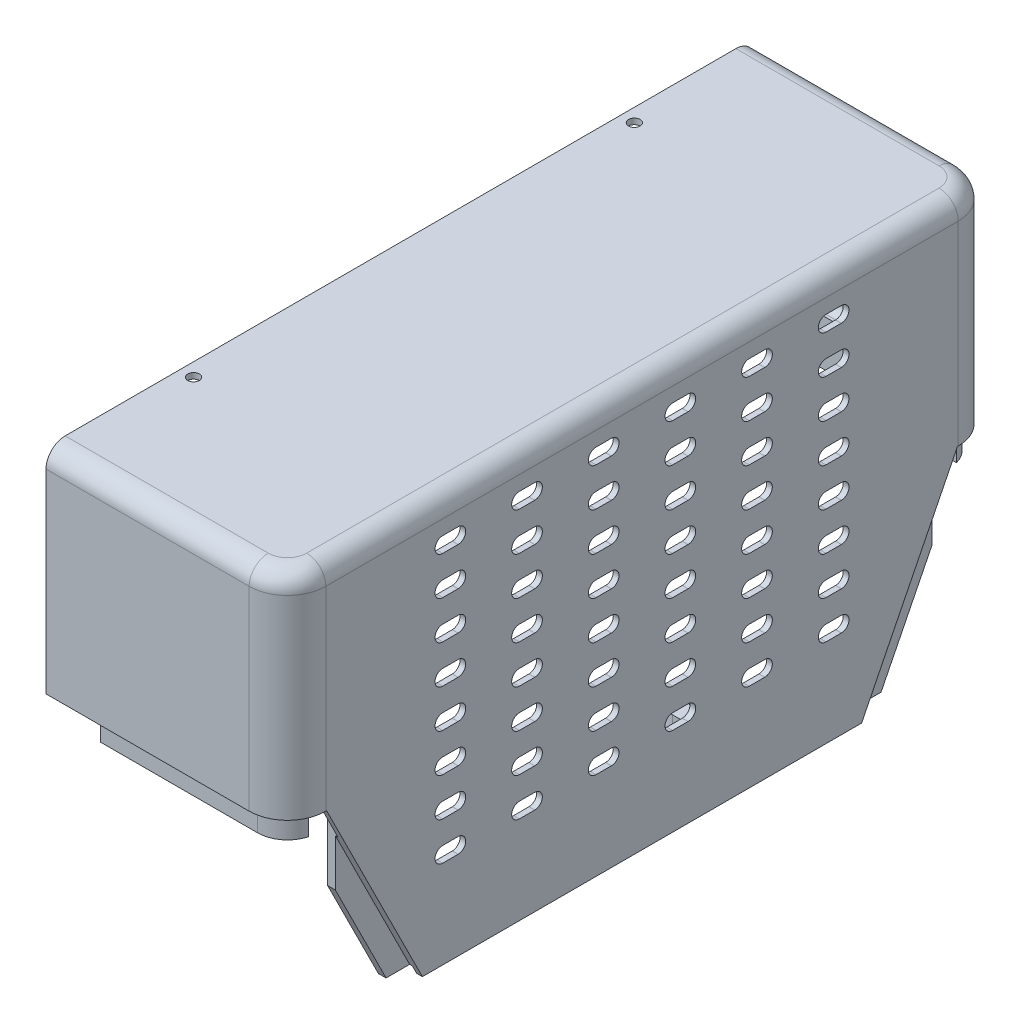
SolidWorks part; units mm, degrees
ref_plane "Alzado" through (0, 0, 0) normal (0, 0, 1) x (1, 0, 0)
ref_plane "Planta" through (0, 0, 0) normal (0, 1, 0) x (1, 0, 0)
ref_plane "Vista lateral" through (0, 0, 0) normal (1, 0, 0) x (0, 0, -1)
sketch "Croquis1" plane through (0, 60.8505, 0) normal (0, 1, 0) x (1, 0, 0)
  line L0 (-39.0358, -277.5) -> (-39.0358, -272.5) construction
  line L1 (-39.0358, -97.5) -> (-39.0358, -92.5) construction
  line L2 (-39.0358, -272.5) -> (-39.0358, -97.5) construction
  line L3 (13.9642, -92.5) -> (-39.0358, -92.5) construction
  line L4 (23.9642, -127.5) -> (23.9642, -102.5) construction
  line L5 (23.9642, -242.5) -> (23.9642, -127.5) construction
  line L6 (23.9642, -267.5) -> (23.9642, -242.5) construction
  line L7 (-39.0358, -277.5) -> (13.9642, -277.5) construction
  line L8 (-39.0358, -277.5) -> (-39.0358, -272.5)
  line L9 (-39.0358, -97.5) -> (-39.0358, -92.5)
  line L10 (-39.0358, -272.5) -> (-39.0358, -97.5)
  line L11 (13.9642, -92.5) -> (-39.0358, -92.5)
  line L12 (23.9642, -127.5) -> (23.9642, -102.5)
  line L13 (23.9642, -242.5) -> (23.9642, -127.5)
  line L14 (23.9642, -267.5) -> (23.9642, -242.5)
  line L15 (-39.0358, -277.5) -> (13.9642, -277.5)
  arc A0 (23.9642, -102.5) -> (13.9642, -92.5) centre (13.9642, -102.5) ccw construction
  arc A1 (13.9642, -277.5) -> (23.9642, -267.5) centre (13.9642, -267.5) ccw construction
  arc A2 (23.9642, -102.5) -> (13.9642, -92.5) centre (13.9642, -102.5) ccw
  arc A3 (13.9642, -277.5) -> (23.9642, -267.5) centre (13.9642, -267.5) ccw
extrude "Saliente-Extruir1" add sketch "Croquis1" against normal blind 1.5
sketch "Croquis2" plane through (0, 59.3505, 0) normal (0, -1, 0) x (1, 0, 0)
  line L0 (13.9642, 92.5) -> (-39.0358, 92.5) construction
  line L1 (23.9642, 267.5) -> (23.9642, 102.5) construction
  line L2 (-39.0358, 277.5) -> (13.9642, 277.5) construction
  line L3 (13.9642, 92.5) -> (-39.0358, 92.5)
  line L4 (23.9642, 267.5) -> (23.9642, 102.5)
  line L5 (-39.0358, 277.5) -> (13.9642, 277.5)
  line L6 (-39.0358, 276) -> (13.9642, 276)
  line L7 (22.4642, 267.5) -> (22.4642, 102.5)
  line L8 (13.9642, 94) -> (-39.0358, 94)
  line L9 (-39.0358, 92.5) -> (-39.0358, 94)
  line L10 (-39.0358, 277.5) -> (-39.0358, 276)
  arc A0 (13.9642, 92.5) -> (23.9642, 102.5) centre (13.9642, 102.5) ccw construction
  arc A1 (23.9642, 267.5) -> (13.9642, 277.5) centre (13.9642, 267.5) ccw construction
  arc A2 (13.9642, 92.5) -> (23.9642, 102.5) centre (13.9642, 102.5) ccw
  arc A3 (23.9642, 267.5) -> (13.9642, 277.5) centre (13.9642, 267.5) ccw
  arc A4 (22.4642, 267.5) -> (13.9642, 276) centre (13.9642, 267.5) ccw
  arc A5 (13.9642, 94) -> (22.4642, 102.5) centre (13.9642, 102.5) ccw
  dimension "D1" = 1.5
extrude "Saliente-Extruir2" add sketch "Croquis2" along normal offset from surface (54.3 mm away) 0.2
sketch "Croquis3" plane through (0, 5.0505, 0) normal (0, -1, 0) x (1, 0, 0)
  line L0 (22.4642, 267.3) -> (23.9642, 267.3)
  line L1 (22.4642, 102.5) -> (22.4642, 267.5) construction
  line L2 (23.9642, 267.5) -> (23.9642, 102.5) construction
  line L3 (23.9642, 267.3) -> (23.9642, 102.7)
  line L4 (23.9642, 102.7) -> (22.4642, 102.7)
  line L5 (22.4642, 102.7) -> (22.4642, 267.3)
  line L6 (21.9642, 267.5) -> (23.9642, 267.5) construction
  line L7 (23.9642, 102.5) -> (21.9642, 102.5) construction
  dimension "D1" = 0.2
  dimension "D2" = 0.2
extrude "Saliente-Extruir3" add sketch "Croquis3" along normal offset from surface (50 mm away) 0.2
sketch "Croquis4" plane through (23.9642, 0, 0) normal (1, 0, 0) x (0, 0, -1)
  line L0 (-267.3, 5.0505) -> (-242.3, -44.9495)
  line L1 (-102.7, -44.9495) -> (-267.3, -44.9495) construction
  line L2 (-242.3, -44.9495) -> (-280.9783, -56.8361)
  line L3 (-280.9783, -56.8361) -> (-267.3, 5.0505)
  line L4 (-102.7, 5.0505) -> (-131.2482, -52.0459)
  line L5 (-131.2482, -52.0459) -> (-85.324, -44.8872)
  line L6 (-85.324, -44.8872) -> (-102.7, 5.0505)
  line L7 (-267.5, 4.8505) -> (-242.5, -45.1495) construction
  line L8 (-127.5, -45.1495) -> (-102.5, 4.8505) construction
extrude "Cortar-Extruir1" cut sketch "Croquis4" against normal blind 14.2
fillet "Redondeo1" radius 5 10 edges at (-12.5358, 60.8505, 277.5) (21.0353, 60.8505, 274.5711) (23.9642, 60.8505, 185) (21.0353, 60.8505, 95.4289) (-12.5358, 59.3505, 276) (19.9746, 59.3505, 273.5104) (22.4642, 59.3505, 185) (19.9746, 59.3505, 96.4896) (-12.5358, 60.8505, 92.5) (-12.5358, 59.3505, 94)
sketch "Croquis5" plane through (0, 5.0505, 0) normal (0, -1, 0) x (1, 0, 0)
  line L0 (-39.0358, 94) -> (13.9642, 94) construction
  line L1 (13.9642, 276) -> (-39.0358, 276) construction
  line L2 (-27.0358, 94) -> (13.9642, 94)
  line L3 (13.9642, 276) -> (-27.0358, 276)
  line L4 (13.9642, 273.3) -> (-27.0358, 273.3)
  line L5 (-27.0358, 276) -> (-27.0358, 273.3)
  line L6 (19.4085, 269.5) -> (22.2256, 269.5)
  line L7 (17.4642, 267.5) -> (22.4642, 267.5) construction
  line L8 (-39.0358, 276) -> (-39.0358, 271) construction
  line L9 (13.9642, 276) -> (-39.0358, 276) construction
  line L10 (13.9642, 273.3) -> (-39.0358, 273.3) construction
  line L11 (-27.0358, 96.7) -> (13.9642, 96.7)
  line L12 (-27.0358, 96.7) -> (-27.0358, 94)
  line L13 (19.4085, 100.5) -> (22.2256, 100.5)
  line L14 (17.4642, 102.5) -> (22.4642, 102.5) construction
  line L16 (-39.0358, 96.7) -> (13.9642, 96.7) construction
  line L17 (-39.0358, 94) -> (13.9642, 94) construction
  arc A0 (13.9642, 94) -> (22.4642, 102.5) centre (13.9642, 102.5) ccw construction
  arc A1 (22.4642, 267.5) -> (13.9642, 276) centre (13.9642, 267.5) ccw construction
  arc A2 (13.9642, 94) -> (22.2256, 100.5) centre (13.9642, 102.5) ccw
  arc A3 (22.2256, 269.5) -> (13.9642, 276) centre (13.9642, 267.5) ccw
  arc A4 (19.4085, 269.5) -> (13.9642, 273.3) centre (13.9642, 267.5) ccw
  arc A5 (19.7642, 267.5) -> (13.9642, 273.3) centre (13.9642, 267.5) ccw construction
  arc A6 (22.4642, 267.5) -> (13.9642, 276) centre (13.9642, 267.5) ccw construction
  arc A7 (13.9642, 96.7) -> (19.4085, 100.5) centre (13.9642, 102.5) ccw
  arc A8 (13.9642, 94) -> (22.4642, 102.5) centre (13.9642, 102.5) ccw construction
  arc A9 (13.9642, 96.7) -> (19.7642, 102.5) centre (13.9642, 102.5) ccw construction
  dimension "D2" = 2
  dimension "D3" = 12
  dimension "D5" = 2
  dimension "D1" = 2.7
  dimension "D4" = 2.7
extrude "Saliente-Extruir4" add sketch "Croquis5" against normal blind 6
sketch "Croquis6" plane through (22.4642, 0, 0) normal (-1, 0, 0) x (0, 0, 1)
  line L0 (242.3, -44.9495) -> (267.3, 5.0505) construction
  line L1 (102.7, 5.0505) -> (127.7, -44.9495) construction
  line L2 (243.418, -42.7134) -> (262.8279, -3.8938)
  line L3 (107.1721, -3.8938) -> (126.582, -42.7134)
  line L11 (237.8279, -42.7134) -> (262.8279, 7.2866)
  line L12 (237.8279, -42.7134) -> (262.8279, 7.2866)
  line L13 (262.8279, 7.2866) -> (262.8279, -3.8938)
  line L16 (107.1721, 7.2866) -> (132.1721, -42.7134)
  line L17 (107.1721, 7.2866) -> (132.1721, -42.7134)
  line L18 (237.8279, -42.7134) -> (243.418, -42.7134)
  line L19 (107.1721, 7.2866) -> (107.1721, -3.8938)
  line L20 (132.1721, -42.7134) -> (126.582, -42.7134)
  dimension "D2" = 5
  dimension "D4" = 5
extrude "Saliente-Extruir5" add sketch "Croquis6" along normal blind 2.7
fillet "Redondeo3" radius 2 2 edges at (22.4642, -17.7134, 250.3279) (22.4642, -17.7134, 119.6721)
sketch "Croquis7" plane through (0, -44.9495, 0) normal (0, -1, 0) x (1, 0, 0)
  line L0 (15.4057, 168.5) -> (22.6426, 168.5)
  line L1 (22.6426, 168.5) -> (22.6426, 156.5)
  line L2 (22.6426, 156.5) -> (15.4057, 156.5)
  circle A0 centre (15.4057, 162.5) radius 1.5
  arc A1 (15.4057, 168.5) -> (15.4057, 156.5) centre (15.4057, 162.5) ccw
extrude "Saliente-Extruir6" add sketch "Croquis7" against normal blind 13 from offset 5 offset against normal yes
fillet "Redondeo4" radius 5 1 edges at (22.4642, -26.9495, 162.5)
sketch "Croquis8" plane through (0, 60.8505, 0) normal (0, 1, 0) x (1, 0, 0)
  line L0 (-39.0358, -185) -> (52.144, -185) construction
  line L1 (-39.0358, -97.5) -> (-39.0358, -272.5) construction
  circle A0 centre (-28.2574, -255) radius 6.5
  circle A1 centre (-28.2574, -115) radius 6.5
  dimension "D1" = 13
  dimension "D2" = 70
sketch "Croquis11" plane through (23.9642, 0, 0) normal (1, 0, 0) x (0, 0, -1)
  line L0 (-185, -44.9495) -> (-185, 76.3507) construction
  line L1 (-127.7, -44.9495) -> (-242.3, -44.9495) construction
  line L2 (-193, -19.9495) -> (-197, -19.9495) construction
  line L3 (-193, -21.9495) -> (-197, -21.9495)
  line L4 (-193, -17.9495) -> (-197, -17.9495)
  line L5 (-213, -19.9495) -> (-217, -19.9495) construction
  line L6 (-213, -21.9495) -> (-217, -21.9495)
  line L7 (-213, -17.9495) -> (-217, -17.9495)
  line L8 (-233, -19.9495) -> (-237, -19.9495) construction
  line L9 (-233, -21.9495) -> (-237, -21.9495)
  line L10 (-233, -17.9495) -> (-237, -17.9495)
  line L11 (-213, -9.9495) -> (-217, -9.9495) construction
  line L12 (-213, -11.9495) -> (-217, -11.9495)
  line L13 (-213, -7.9495) -> (-217, -7.9495)
  line L14 (-233, -9.9495) -> (-237, -9.9495) construction
  line L15 (-233, -11.9495) -> (-237, -11.9495)
  line L16 (-233, -7.9495) -> (-237, -7.9495)
  line L17 (-213, 0.0505) -> (-217, 0.0505) construction
  line L18 (-213, -1.9495) -> (-217, -1.9495)
  line L19 (-213, 2.0505) -> (-217, 2.0505)
  line L20 (-233, 0.0505) -> (-237, 0.0505) construction
  line L21 (-233, -1.9495) -> (-237, -1.9495)
  line L22 (-233, 2.0505) -> (-237, 2.0505)
  line L23 (-213, 10.0505) -> (-217, 10.0505) construction
  line L24 (-213, 8.0505) -> (-217, 8.0505)
  line L25 (-213, 12.0505) -> (-217, 12.0505)
  line L26 (-233, 10.0505) -> (-237, 10.0505) construction
  line L27 (-233, 8.0505) -> (-237, 8.0505)
  line L28 (-233, 12.0505) -> (-237, 12.0505)
  line L29 (-213, 20.0505) -> (-217, 20.0505) construction
  line L30 (-213, 18.0505) -> (-217, 18.0505)
  line L31 (-213, 22.0505) -> (-217, 22.0505)
  line L32 (-233, 20.0505) -> (-237, 20.0505) construction
  line L33 (-233, 18.0505) -> (-237, 18.0505)
  line L34 (-233, 22.0505) -> (-237, 22.0505)
  line L35 (-213, 30.0505) -> (-217, 30.0505) construction
  line L36 (-213, 28.0505) -> (-217, 28.0505)
  line L37 (-213, 32.0505) -> (-217, 32.0505)
  line L38 (-233, 30.0505) -> (-237, 30.0505) construction
  line L39 (-233, 28.0505) -> (-237, 28.0505)
  line L40 (-233, 32.0505) -> (-237, 32.0505)
  line L41 (-213, 40.0505) -> (-217, 40.0505) construction
  line L42 (-213, 38.0505) -> (-217, 38.0505)
  line L43 (-213, 42.0505) -> (-217, 42.0505)
  line L44 (-233, 40.0505) -> (-237, 40.0505) construction
  line L45 (-233, 38.0505) -> (-237, 38.0505)
  line L46 (-233, 42.0505) -> (-237, 42.0505)
  line L47 (-213, 50.0505) -> (-217, 50.0505) construction
  line L48 (-213, 48.0505) -> (-217, 48.0505)
  line L49 (-213, 52.0505) -> (-217, 52.0505)
  line L50 (-233, 50.0505) -> (-237, 50.0505) construction
  line L51 (-233, 48.0505) -> (-237, 48.0505)
  line L52 (-233, 52.0505) -> (-237, 52.0505)
  line L53 (-193, -9.9495) -> (-197, -9.9495) construction
  line L54 (-193, -11.9495) -> (-197, -11.9495)
  line L55 (-193, -7.9495) -> (-197, -7.9495)
  line L56 (-193, 0.0505) -> (-197, 0.0505) construction
  line L57 (-193, -1.9495) -> (-197, -1.9495)
  line L58 (-193, 2.0505) -> (-197, 2.0505)
  line L59 (-193, 10.0505) -> (-197, 10.0505) construction
  line L60 (-193, 8.0505) -> (-197, 8.0505)
  line L61 (-193, 12.0505) -> (-197, 12.0505)
  line L62 (-193, 20.0505) -> (-197, 20.0505) construction
  line L63 (-193, 18.0505) -> (-197, 18.0505)
  line L64 (-193, 22.0505) -> (-197, 22.0505)
  line L65 (-193, 30.0505) -> (-197, 30.0505) construction
  line L66 (-193, 28.0505) -> (-197, 28.0505)
  line L67 (-193, 32.0505) -> (-197, 32.0505)
  line L68 (-193, 40.0505) -> (-197, 40.0505) construction
  line L69 (-193, 38.0505) -> (-197, 38.0505)
  line L70 (-193, 42.0505) -> (-197, 42.0505)
  line L71 (-193, 50.0505) -> (-197, 50.0505) construction
  line L72 (-193, 48.0505) -> (-197, 48.0505)
  line L73 (-193, 52.0505) -> (-197, 52.0505)
  line L74 (-199, -19.9495) -> (-211, -19.9495) construction
  line L75 (-171, -19.9495) -> (-159, -19.9495) construction
  line L76 (-177, 50.0505) -> (-173, 50.0505) construction
  line L77 (-177, 48.0505) -> (-173, 48.0505)
  line L78 (-177, 52.0505) -> (-173, 52.0505)
  line L79 (-177, 40.0505) -> (-173, 40.0505) construction
  line L80 (-177, 38.0505) -> (-173, 38.0505)
  line L81 (-177, 42.0505) -> (-173, 42.0505)
  line L82 (-177, 30.0505) -> (-173, 30.0505) construction
  line L83 (-177, 28.0505) -> (-173, 28.0505)
  line L84 (-177, 32.0505) -> (-173, 32.0505)
  line L85 (-177, 20.0505) -> (-173, 20.0505) construction
  line L86 (-177, 18.0505) -> (-173, 18.0505)
  line L87 (-177, 22.0505) -> (-173, 22.0505)
  line L88 (-177, 10.0505) -> (-173, 10.0505) construction
  line L89 (-177, 8.0505) -> (-173, 8.0505)
  line L90 (-177, 12.0505) -> (-173, 12.0505)
  line L91 (-177, 0.0505) -> (-173, 0.0505) construction
  line L92 (-177, -1.9495) -> (-173, -1.9495)
  line L93 (-177, 2.0505) -> (-173, 2.0505)
  line L94 (-177, -9.9495) -> (-173, -9.9495) construction
  line L95 (-177, -11.9495) -> (-173, -11.9495)
  line L96 (-177, -7.9495) -> (-173, -7.9495)
  line L97 (-137, 50.0505) -> (-133, 50.0505) construction
  line L98 (-137, 48.0505) -> (-133, 48.0505)
  line L99 (-137, 52.0505) -> (-133, 52.0505)
  line L100 (-157, 50.0505) -> (-153, 50.0505) construction
  line L101 (-157, 48.0505) -> (-153, 48.0505)
  line L102 (-157, 52.0505) -> (-153, 52.0505)
  line L103 (-137, 40.0505) -> (-133, 40.0505) construction
  line L104 (-137, 38.0505) -> (-133, 38.0505)
  line L105 (-137, 42.0505) -> (-133, 42.0505)
  line L106 (-157, 40.0505) -> (-153, 40.0505) construction
  line L107 (-157, 38.0505) -> (-153, 38.0505)
  line L108 (-157, 42.0505) -> (-153, 42.0505)
  line L109 (-137, 30.0505) -> (-133, 30.0505) construction
  line L110 (-137, 28.0505) -> (-133, 28.0505)
  line L111 (-137, 32.0505) -> (-133, 32.0505)
  line L112 (-157, 30.0505) -> (-153, 30.0505) construction
  line L113 (-157, 28.0505) -> (-153, 28.0505)
  line L114 (-157, 32.0505) -> (-153, 32.0505)
  line L115 (-137, 20.0505) -> (-133, 20.0505) construction
  line L116 (-137, 18.0505) -> (-133, 18.0505)
  line L117 (-137, 22.0505) -> (-133, 22.0505)
  line L118 (-157, 20.0505) -> (-153, 20.0505) construction
  line L119 (-157, 18.0505) -> (-153, 18.0505)
  line L120 (-157, 22.0505) -> (-153, 22.0505)
  line L121 (-137, 10.0505) -> (-133, 10.0505) construction
  line L122 (-137, 8.0505) -> (-133, 8.0505)
  line L123 (-137, 12.0505) -> (-133, 12.0505)
  line L124 (-157, 10.0505) -> (-153, 10.0505) construction
  line L125 (-157, 8.0505) -> (-153, 8.0505)
  line L126 (-157, 12.0505) -> (-153, 12.0505)
  line L127 (-137, 0.0505) -> (-133, 0.0505) construction
  line L128 (-137, -1.9495) -> (-133, -1.9495)
  line L129 (-137, 2.0505) -> (-133, 2.0505)
  line L130 (-157, 0.0505) -> (-153, 0.0505) construction
  line L131 (-157, -1.9495) -> (-153, -1.9495)
  line L132 (-157, 2.0505) -> (-153, 2.0505)
  line L133 (-137, -9.9495) -> (-133, -9.9495) construction
  line L134 (-137, -11.9495) -> (-133, -11.9495)
  line L135 (-137, -7.9495) -> (-133, -7.9495)
  line L136 (-157, -9.9495) -> (-153, -9.9495) construction
  line L137 (-157, -11.9495) -> (-153, -11.9495)
  line L138 (-157, -7.9495) -> (-153, -7.9495)
  line L139 (-137, -19.9495) -> (-133, -19.9495) construction
  line L140 (-137, -21.9495) -> (-133, -21.9495)
  line L141 (-137, -17.9495) -> (-133, -17.9495)
  line L142 (-157, -19.9495) -> (-153, -19.9495) construction
  line L143 (-157, -21.9495) -> (-153, -21.9495)
  line L144 (-157, -17.9495) -> (-153, -17.9495)
  line L145 (-177, -19.9495) -> (-173, -19.9495) construction
  line L146 (-177, -21.9495) -> (-173, -21.9495)
  line L147 (-177, -17.9495) -> (-173, -17.9495)
  arc A0 (-193, -21.9495) -> (-193, -17.9495) centre (-193, -19.9495) ccw
  arc A1 (-197, -17.9495) -> (-197, -21.9495) centre (-197, -19.9495) ccw
  arc A2 (-213, -21.9495) -> (-213, -17.9495) centre (-213, -19.9495) ccw
  arc A3 (-217, -17.9495) -> (-217, -21.9495) centre (-217, -19.9495) ccw
  arc A4 (-233, -21.9495) -> (-233, -17.9495) centre (-233, -19.9495) ccw
  arc A5 (-237, -17.9495) -> (-237, -21.9495) centre (-237, -19.9495) ccw
  arc A6 (-213, -11.9495) -> (-213, -7.9495) centre (-213, -9.9495) ccw
  arc A7 (-217, -7.9495) -> (-217, -11.9495) centre (-217, -9.9495) ccw
  arc A8 (-233, -11.9495) -> (-233, -7.9495) centre (-233, -9.9495) ccw
  arc A9 (-237, -7.9495) -> (-237, -11.9495) centre (-237, -9.9495) ccw
  arc A10 (-213, -1.9495) -> (-213, 2.0505) centre (-213, 0.0505) ccw
  arc A11 (-217, 2.0505) -> (-217, -1.9495) centre (-217, 0.0505) ccw
  arc A12 (-233, -1.9495) -> (-233, 2.0505) centre (-233, 0.0505) ccw
  arc A13 (-237, 2.0505) -> (-237, -1.9495) centre (-237, 0.0505) ccw
  arc A14 (-213, 8.0505) -> (-213, 12.0505) centre (-213, 10.0505) ccw
  arc A15 (-217, 12.0505) -> (-217, 8.0505) centre (-217, 10.0505) ccw
  arc A16 (-233, 8.0505) -> (-233, 12.0505) centre (-233, 10.0505) ccw
  arc A17 (-237, 12.0505) -> (-237, 8.0505) centre (-237, 10.0505) ccw
  arc A18 (-213, 18.0505) -> (-213, 22.0505) centre (-213, 20.0505) ccw
  arc A19 (-217, 22.0505) -> (-217, 18.0505) centre (-217, 20.0505) ccw
  arc A20 (-233, 18.0505) -> (-233, 22.0505) centre (-233, 20.0505) ccw
  arc A21 (-237, 22.0505) -> (-237, 18.0505) centre (-237, 20.0505) ccw
  arc A22 (-213, 28.0505) -> (-213, 32.0505) centre (-213, 30.0505) ccw
  arc A23 (-217, 32.0505) -> (-217, 28.0505) centre (-217, 30.0505) ccw
  arc A24 (-233, 28.0505) -> (-233, 32.0505) centre (-233, 30.0505) ccw
  arc A25 (-237, 32.0505) -> (-237, 28.0505) centre (-237, 30.0505) ccw
  arc A26 (-213, 38.0505) -> (-213, 42.0505) centre (-213, 40.0505) ccw
  arc A27 (-217, 42.0505) -> (-217, 38.0505) centre (-217, 40.0505) ccw
  arc A28 (-233, 38.0505) -> (-233, 42.0505) centre (-233, 40.0505) ccw
  arc A29 (-237, 42.0505) -> (-237, 38.0505) centre (-237, 40.0505) ccw
  arc A30 (-213, 48.0505) -> (-213, 52.0505) centre (-213, 50.0505) ccw
  arc A31 (-217, 52.0505) -> (-217, 48.0505) centre (-217, 50.0505) ccw
  arc A32 (-233, 48.0505) -> (-233, 52.0505) centre (-233, 50.0505) ccw
  arc A33 (-237, 52.0505) -> (-237, 48.0505) centre (-237, 50.0505) ccw
  arc A34 (-193, -11.9495) -> (-193, -7.9495) centre (-193, -9.9495) ccw
  arc A35 (-197, -7.9495) -> (-197, -11.9495) centre (-197, -9.9495) ccw
  arc A36 (-193, -1.9495) -> (-193, 2.0505) centre (-193, 0.0505) ccw
  arc A37 (-197, 2.0505) -> (-197, -1.9495) centre (-197, 0.0505) ccw
  arc A38 (-193, 8.0505) -> (-193, 12.0505) centre (-193, 10.0505) ccw
  arc A39 (-197, 12.0505) -> (-197, 8.0505) centre (-197, 10.0505) ccw
  arc A40 (-193, 18.0505) -> (-193, 22.0505) centre (-193, 20.0505) ccw
  arc A41 (-197, 22.0505) -> (-197, 18.0505) centre (-197, 20.0505) ccw
  arc A42 (-193, 28.0505) -> (-193, 32.0505) centre (-193, 30.0505) ccw
  arc A43 (-197, 32.0505) -> (-197, 28.0505) centre (-197, 30.0505) ccw
  arc A44 (-193, 38.0505) -> (-193, 42.0505) centre (-193, 40.0505) ccw
  arc A45 (-197, 42.0505) -> (-197, 38.0505) centre (-197, 40.0505) ccw
  arc A46 (-193, 48.0505) -> (-193, 52.0505) centre (-193, 50.0505) ccw
  arc A47 (-197, 52.0505) -> (-197, 48.0505) centre (-197, 50.0505) ccw
  arc A48 (-177, 48.0505) -> (-177, 52.0505) centre (-177, 50.0505) cw
  arc A49 (-173, 52.0505) -> (-173, 48.0505) centre (-173, 50.0505) cw
  arc A50 (-177, 38.0505) -> (-177, 42.0505) centre (-177, 40.0505) cw
  arc A51 (-173, 42.0505) -> (-173, 38.0505) centre (-173, 40.0505) cw
  arc A52 (-177, 28.0505) -> (-177, 32.0505) centre (-177, 30.0505) cw
  arc A53 (-173, 32.0505) -> (-173, 28.0505) centre (-173, 30.0505) cw
  arc A54 (-177, 18.0505) -> (-177, 22.0505) centre (-177, 20.0505) cw
  arc A55 (-173, 22.0505) -> (-173, 18.0505) centre (-173, 20.0505) cw
  arc A56 (-177, 8.0505) -> (-177, 12.0505) centre (-177, 10.0505) cw
  arc A57 (-173, 12.0505) -> (-173, 8.0505) centre (-173, 10.0505) cw
  arc A58 (-177, -1.9495) -> (-177, 2.0505) centre (-177, 0.0505) cw
  arc A59 (-173, 2.0505) -> (-173, -1.9495) centre (-173, 0.0505) cw
  arc A60 (-177, -11.9495) -> (-177, -7.9495) centre (-177, -9.9495) cw
  arc A61 (-173, -7.9495) -> (-173, -11.9495) centre (-173, -9.9495) cw
  arc A62 (-137, 48.0505) -> (-137, 52.0505) centre (-137, 50.0505) cw
  arc A63 (-133, 52.0505) -> (-133, 48.0505) centre (-133, 50.0505) cw
  arc A64 (-157, 48.0505) -> (-157, 52.0505) centre (-157, 50.0505) cw
  arc A65 (-153, 52.0505) -> (-153, 48.0505) centre (-153, 50.0505) cw
  arc A66 (-137, 38.0505) -> (-137, 42.0505) centre (-137, 40.0505) cw
  arc A67 (-133, 42.0505) -> (-133, 38.0505) centre (-133, 40.0505) cw
  arc A68 (-157, 38.0505) -> (-157, 42.0505) centre (-157, 40.0505) cw
  arc A69 (-153, 42.0505) -> (-153, 38.0505) centre (-153, 40.0505) cw
  arc A70 (-137, 28.0505) -> (-137, 32.0505) centre (-137, 30.0505) cw
  arc A71 (-133, 32.0505) -> (-133, 28.0505) centre (-133, 30.0505) cw
  arc A72 (-157, 28.0505) -> (-157, 32.0505) centre (-157, 30.0505) cw
  arc A73 (-153, 32.0505) -> (-153, 28.0505) centre (-153, 30.0505) cw
  arc A74 (-137, 18.0505) -> (-137, 22.0505) centre (-137, 20.0505) cw
  arc A75 (-133, 22.0505) -> (-133, 18.0505) centre (-133, 20.0505) cw
  arc A76 (-157, 18.0505) -> (-157, 22.0505) centre (-157, 20.0505) cw
  arc A77 (-153, 22.0505) -> (-153, 18.0505) centre (-153, 20.0505) cw
  arc A78 (-137, 8.0505) -> (-137, 12.0505) centre (-137, 10.0505) cw
  arc A79 (-133, 12.0505) -> (-133, 8.0505) centre (-133, 10.0505) cw
  arc A80 (-157, 8.0505) -> (-157, 12.0505) centre (-157, 10.0505) cw
  arc A81 (-153, 12.0505) -> (-153, 8.0505) centre (-153, 10.0505) cw
  arc A82 (-137, -1.9495) -> (-137, 2.0505) centre (-137, 0.0505) cw
  arc A83 (-133, 2.0505) -> (-133, -1.9495) centre (-133, 0.0505) cw
  arc A84 (-157, -1.9495) -> (-157, 2.0505) centre (-157, 0.0505) cw
  arc A85 (-153, 2.0505) -> (-153, -1.9495) centre (-153, 0.0505) cw
  arc A86 (-137, -11.9495) -> (-137, -7.9495) centre (-137, -9.9495) cw
  arc A87 (-133, -7.9495) -> (-133, -11.9495) centre (-133, -9.9495) cw
  arc A88 (-157, -11.9495) -> (-157, -7.9495) centre (-157, -9.9495) cw
  arc A89 (-153, -7.9495) -> (-153, -11.9495) centre (-153, -9.9495) cw
  arc A90 (-137, -21.9495) -> (-137, -17.9495) centre (-137, -19.9495) cw
  arc A91 (-133, -17.9495) -> (-133, -21.9495) centre (-133, -19.9495) cw
  arc A92 (-157, -21.9495) -> (-157, -17.9495) centre (-157, -19.9495) cw
  arc A93 (-153, -17.9495) -> (-153, -21.9495) centre (-153, -19.9495) cw
  arc A94 (-177, -21.9495) -> (-177, -17.9495) centre (-177, -19.9495) cw
  arc A95 (-173, -17.9495) -> (-173, -21.9495) centre (-173, -19.9495) cw
  point P6 (-195, -19.9495)
  point P15 (-215, -19.9495)
  point P22 (-235, -19.9495)
  point P29 (-215, -9.9495)
  point P36 (-235, -9.9495)
  point P43 (-215, 0.0505)
  point P50 (-235, 0.0505)
  point P57 (-215, 10.0505)
  point P64 (-235, 10.0505)
  point P71 (-215, 20.0505)
  point P78 (-235, 20.0505)
  point P85 (-215, 30.0505)
  point P92 (-235, 30.0505)
  point P99 (-215, 40.0505)
  point P106 (-235, 40.0505)
  point P113 (-215, 50.0505)
  point P120 (-235, 50.0505)
  point P127 (-195, -9.9495)
  point P134 (-195, 0.0505)
  point P141 (-195, 10.0505)
  point P148 (-195, 20.0505)
  point P155 (-195, 30.0505)
  point P162 (-195, 40.0505)
  point P169 (-195, 50.0505)
  point P178 (-175, 50.0505)
  point P185 (-175, 40.0505)
  point P192 (-175, 30.0505)
  point P199 (-175, 20.0505)
  point P206 (-175, 10.0505)
  point P213 (-175, 0.0505)
  point P220 (-175, -9.9495)
  point P227 (-135, 50.0505)
  point P234 (-155, 50.0505)
  point P241 (-135, 40.0505)
  point P248 (-155, 40.0505)
  point P255 (-135, 30.0505)
  point P262 (-155, 30.0505)
  point P269 (-135, 20.0505)
  point P276 (-155, 20.0505)
  point P283 (-135, 10.0505)
  point P290 (-155, 10.0505)
  point P297 (-135, 0.0505)
  point P304 (-155, 0.0505)
  point P311 (-135, -9.9495)
  point P318 (-155, -9.9495)
  point P325 (-135, -19.9495)
  point P332 (-155, -19.9495)
  point P339 (-175, -19.9495)
  dimension "D2" = 2
  dimension "D1" = 4
  dimension "D3" = 8
  dimension "D4" = 25
  dimension "D5" = 3
  dimension "D6" = 8
extrude "Cortar-Extruir4" cut sketch "Croquis11" against normal blind 6
sketch "Croquis12" plane through (0, 5.0505, 0) normal (0, -1, 0) x (1, 0, 0)
  line L4 (-27.0358, 273.3) -> (13.9642, 273.3) construction
  line L5 (13.9642, 275.3) -> (-39.0358, 275.3)
  line L6 (13.9642, 275.3) -> (-27.0358, 275.3)
  line L7 (-27.0358, 273.3) -> (13.9642, 273.3)
  line L9 (19.4085, 269.5) -> (21.5035, 269.5)
  line L12 (13.9642, 96.7) -> (-27.0358, 96.7) construction
  line L13 (13.9642, 94.7) -> (-39.0358, 94.7)
  line L14 (13.9642, 94.7) -> (-27.0358, 94.7)
  line L15 (13.9642, 96.7) -> (-27.0358, 96.7)
  line L17 (19.4085, 100.5) -> (21.5035, 100.5)
  line L18 (-27.0358, 96.7) -> (-27.0358, 94.7)
  line L19 (-27.0358, 273.3) -> (-27.0358, 275.3)
  arc A5 (19.4085, 269.5) -> (13.9642, 273.3) centre (13.9642, 267.5) ccw construction
  arc A6 (21.7642, 267.5) -> (13.9642, 275.3) centre (13.9642, 267.5) ccw
  arc A7 (21.5035, 269.5) -> (13.9642, 275.3) centre (13.9642, 267.5) ccw
  arc A8 (19.4085, 269.5) -> (13.9642, 273.3) centre (13.9642, 267.5) ccw
  arc A10 (13.9642, 96.7) -> (19.4085, 100.5) centre (13.9642, 102.5) ccw construction
  arc A11 (13.9642, 94.7) -> (21.7642, 102.5) centre (13.9642, 102.5) ccw
  arc A12 (13.9642, 94.7) -> (21.5035, 100.5) centre (13.9642, 102.5) ccw
  arc A13 (13.9642, 96.7) -> (19.4085, 100.5) centre (13.9642, 102.5) ccw
  dimension "D1" = 2.2
  dimension "D2" = 2.2
extrude "Saliente-Extruir7" add sketch "Croquis12" along normal blind 6
sketch "Croquis13" plane through (19.7642, 0, 0) normal (-1, 0, 0) x (0, 0, 1)
  line L0 (107.1721, -3.8938) -> (107.1721, -16.1921)
  line L1 (107.1721, -16.1921) -> (120.4328, -42.7134)
  line L2 (120.4328, -42.7134) -> (126.582, -42.7134)
  line L3 (107.1721, -3.8938) -> (126.582, -42.7134)
  line L4 (243.418, -42.7134) -> (262.8279, -3.8938)
  line L5 (262.8279, -3.8938) -> (262.8279, -16.1921)
  line L6 (262.8279, -16.1921) -> (249.5672, -42.7134)
  line L7 (249.5672, -42.7134) -> (243.418, -42.7134)
  dimension "D1" = 5.5
  dimension "D2" = 5.5
extrude "Saliente-Extruir8" add sketch "Croquis13" against normal blind 2
fillet "Redondeo5" radius 2 4 edges at (-6.5358, 11.0505, 94) (19.2202, 11.0505, 274.1802) (19.2202, 11.0505, 95.8198) (-6.5358, 11.0505, 276)
ref_plane "Plano1" through (-7.5358, 0, 0) normal (-1, 0, 0) x (0, 0, 1)
sketch "Croquis14" plane through (-7.5358, 0, 0) normal (-1, 0, 0) x (0, 0, 1)
  line L0 (276, 5.0505) -> (276, 54.3505) construction
  line L1 (99, 59.3505) -> (271, 59.3505) construction
  line L2 (94, 5.0505) -> (94, 54.3505) construction
  line L3 (276, 8.9383) -> (276, 54.3505)
  line L4 (99, 59.3505) -> (271, 59.3505)
  line L5 (94, 8.9383) -> (94, 54.3505)
  line L6 (96, 8.9383) -> (96, 54.3505)
  line L7 (99, 57.3505) -> (271, 57.3505)
  line L8 (274, 8.9383) -> (274, 54.3505)
  line L9 (94, 8.9383) -> (96, 8.9383)
  line L10 (94, 5.0505) -> (94, 54.3505) construction
  line L11 (96, 5.0505) -> (96, 54.3505) construction
  line L12 (274, 8.9383) -> (276, 8.9383)
  line L13 (274, 5.0505) -> (274, 54.3505) construction
  line L14 (276, 5.0505) -> (276, 54.3505) construction
  arc A0 (276, 54.3505) -> (271, 59.3505) centre (271, 54.3505) ccw construction
  arc A1 (99, 59.3505) -> (94, 54.3505) centre (99, 54.3505) ccw construction
  arc A2 (276, 54.3505) -> (271, 59.3505) centre (271, 54.3505) ccw
  arc A3 (99, 59.3505) -> (94, 54.3505) centre (99, 54.3505) ccw
  arc A4 (99, 57.3505) -> (96, 54.3505) centre (99, 54.3505) ccw
  arc A5 (274, 54.3505) -> (271, 57.3505) centre (271, 54.3505) ccw
  dimension "D1" = 2
extrude "Saliente-Extruir9" add sketch "Croquis14" along normal blind 2.5 and the other way blind 2.5
ref_plane "Plano2" through (0, 0, 165) normal (0, 0, -1) x (-1, 0, 0)
sketch "Croquis15" plane through (0, 0, 165) normal (0, 0, -1) x (-1, 0, 0)
  line L0 (5.0358, 59.3505) -> (-17.4642, 59.3505)
  line L1 (-22.4642, 5.0505) -> (-22.4642, 54.3505) construction
  line L2 (-22.4642, 54.3505) -> (-22.4642, -28.2264)
  line L3 (-22.4642, -28.2264) -> (-20.4642, -28.2264)
  line L4 (-20.4642, -28.2264) -> (-20.4642, 54.3505)
  line L5 (-22.4642, 54.3505) -> (-13.9642, 54.3505) construction
  line L6 (-17.4642, 57.3505) -> (5.0358, 57.3505)
  line L7 (5.0358, 59.3505) -> (5.0358, 57.3505)
  arc A0 (-17.4642, 59.3505) -> (-22.4642, 54.3505) centre (-17.4642, 54.3505) ccw
  arc A1 (-20.4642, 54.3505) -> (-17.4642, 57.3505) centre (-17.4642, 54.3505) cw
  dimension "D1" = 2
  dimension "D2" = 2
extrude "Saliente-Extruir10" add sketch "Croquis15" along normal blind 2.5 and the other way blind 2.5 contours L4 A1 L6 L7 L0 A0 L2 L3
ref_plane "Plano3" through (0, 0, 205) normal (0, 0, 1) x (1, 0, 0)
sketch "Croquis16" plane through (0, 0, 205) normal (0, 0, 1) x (1, 0, 0)
  line L0 (-5.0358, 59.3505) -> (17.4642, 59.3505)
  line L1 (13.9642, 54.3505) -> (22.4642, 54.3505) construction
  line L2 (22.4642, 54.3505) -> (22.4642, -36.0731)
  line L3 (22.4642, -42.7134) -> (22.4642, 11.7587) construction
  line L4 (22.4642, -36.0731) -> (20.4642, -36.0731)
  line L5 (20.4642, -36.0731) -> (20.4642, 54.3505)
  line L6 (17.4642, 57.3505) -> (-5.0358, 57.3505)
  line L8 (-5.0358, 57.3505) -> (-5.0358, 59.3505)
  arc A0 (17.4642, 59.3505) -> (22.4642, 54.3505) centre (17.4642, 54.3505) cw
  arc A1 (20.4642, 54.3505) -> (17.4642, 57.3505) centre (17.4642, 54.3505) ccw
  dimension "D1" = 2
  dimension "D2" = 2
extrude "Saliente-Extruir11" add sketch "Croquis16" along normal blind 2.5 and the other way blind 2.5
sketch "Croquis17" plane through (0, 60.8505, 0) normal (0, 1, 0) x (1, 0, 0)
  line L0 (-39.0358, -185) -> (-32.0358, -185) construction
  line L1 (-39.0358, -97.5) -> (-39.0358, -272.5) construction
  line L2 (-32.0358, -270.5) -> (-32.0358, -99.5) construction
  line L5 (-35.5358, -185) -> (-35.5358, -242.5) construction
  line L6 (13.9642, -277.5) -> (-39.0358, -277.5) construction
  circle A0 centre (-35.5358, -242.5) radius 1.5
  circle A1 centre (-35.5358, -127.5) radius 1.5
  dimension "D2" = 3
  dimension "D1" = 35
extrude "Cortar-Extruir5" cut sketch "Croquis17" against normal blind 19.5
